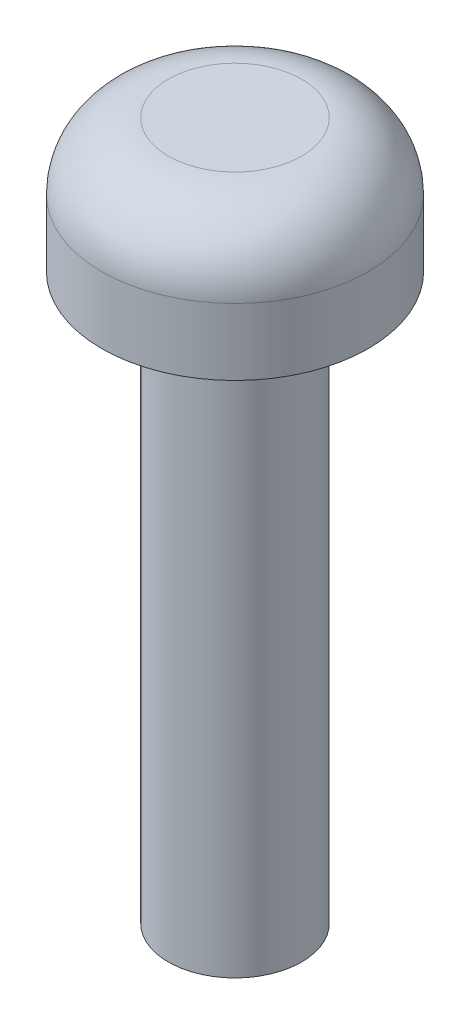
SolidWorks part; units mm, degrees
ref_plane "Front Plane" through (0, 0, 0) normal (0, 0, 1) x (1, 0, 0)
ref_plane "Top Plane" through (0, 0, 0) normal (0, 1, 0) x (1, 0, 0)
ref_plane "Right Plane" through (0, 0, 0) normal (1, 0, 0) x (0, 0, -1)
sketch "Sketch1" plane through (0, 0, 0) normal (0, 1, 0) x (1, 0, 0)
  circle A0 centre (0, 0) radius 3
  dimension "D1" = 6
extrude "Boss-Extrude1" add sketch "Sketch1" along normal blind 3
fillet "Fillet1" radius 1.5 1 edges at (0, 3, 3)
sketch "Sketch2" plane through (0, 0, 0) normal (0, -1, 0) x (1, 0, 0)
  circle A0 centre (0, 0) radius 1.5
  dimension "D1" = 3
extrude "Boss-Extrude2" add sketch "Sketch2" along normal blind 12.7
